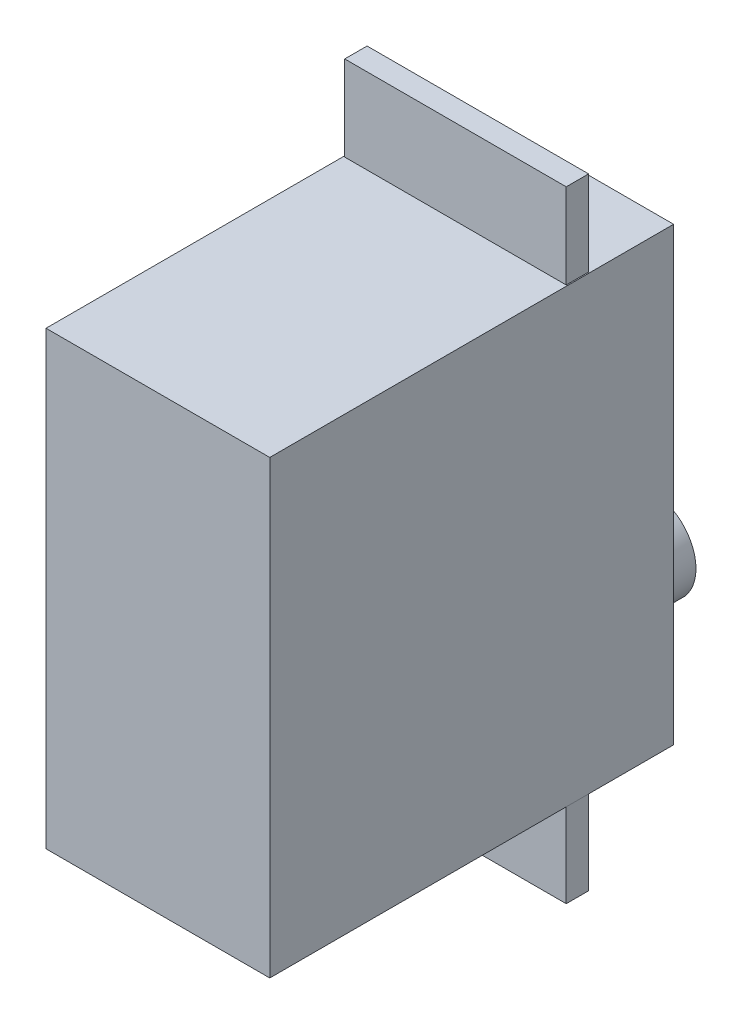
SolidWorks part; units mm, degrees
ref_plane "XY" through (0, 0, 0) normal (0, 0, 1) x (1, 0, 0)
ref_plane "XZ" through (0, 0, 0) normal (0, 1, 0) x (1, 0, 0)
ref_plane "YZ" through (0, 0, 0) normal (1, 0, 0) x (0, 0, -1)
sketch "Esquisse1" plane through (0, 0, 0) normal (0, 0, 1) x (1, 0, 0)
  line L0 (-10, 20.15) -> (10, -20.15) construction
  line L1 (-10, 20.15) -> (10, 20.15)
  line L2 (-10, 20.15) -> (-10, -20.15)
  line L3 (-10, -20.15) -> (10, -20.15)
  line L4 (10, 20.15) -> (10, -20.15)
  dimension "D1" = 20
  dimension "D2" = 40.3
extrude "Boss.-Extru.1" add sketch "Esquisse1" along normal blind 36.1
ref_plane "Plan1" through (-10, -20.15, 0) normal (0, -1, 0) x (1, 0, 0)
sketch "Esquisse3" plane through (-10, -20.15, 0) normal (0, -1, 0) x (1, 0, 0)
  line L1 (19.9, 7.5) -> (0.1, 7.5)
  line L2 (19.9, 7.5) -> (19.9, 9.5)
  line L3 (19.9, 9.5) -> (0.1, 9.5)
  line L4 (0.1, 7.5) -> (0.1, 9.5)
  line L6 (0, 36.1) -> (20, 36.1) construction
  line L7 (20, 36.1) -> (20, 0) construction
  dimension "D1" = 26.6
  dimension "D2" = 19.8
  dimension "D3" = 0.1
  dimension "D4" = 2
extrude "Boss.-Extru.3" add sketch "Esquisse3" along normal blind 7.6
sketch "Esquisse5" plane through (0, 20.15, 0) normal (0, 1, 0) x (1, 0, 0)
  line L0 (9.9, -7.5) -> (9.9, -9.5) construction
  line L1 (-9.9, -7.5) -> (9.9, -7.5)
  line L2 (-9.9, -7.5) -> (-9.9, -9.5)
  line L3 (-9.9, -9.5) -> (9.9, -9.5)
  line L4 (9.9, -7.5) -> (9.9, -9.5)
  line L5 (9.9, -9.5) -> (-9.9, -9.5) construction
  dimension "D1" = 19.8
extrude "Boss.-Extru.4" add sketch "Esquisse5" along normal blind 7.6
sketch "Esquisse6" plane through (0, 0, 0) normal (0, 0, -1) x (-1, 0, 0)
  line L0 (0, 0) -> (0, -29.5077) construction
  circle A0 centre (0, -13.5) radius 4
  dimension "D1" = 8
  dimension "D2" = 13.5
extrude "Boss.-Extru.5" add sketch "Esquisse6" along normal blind 8
sketch "Esquisse7" plane through (0, 0, -8) normal (0, 0, -1) x (-1, 0, 0)
  circle A0 centre (0, -13.5) radius 8.6829
extrude "Boss.-Extru.6" [suppressed] add sketch "Esquisse7" against normal blind 2
